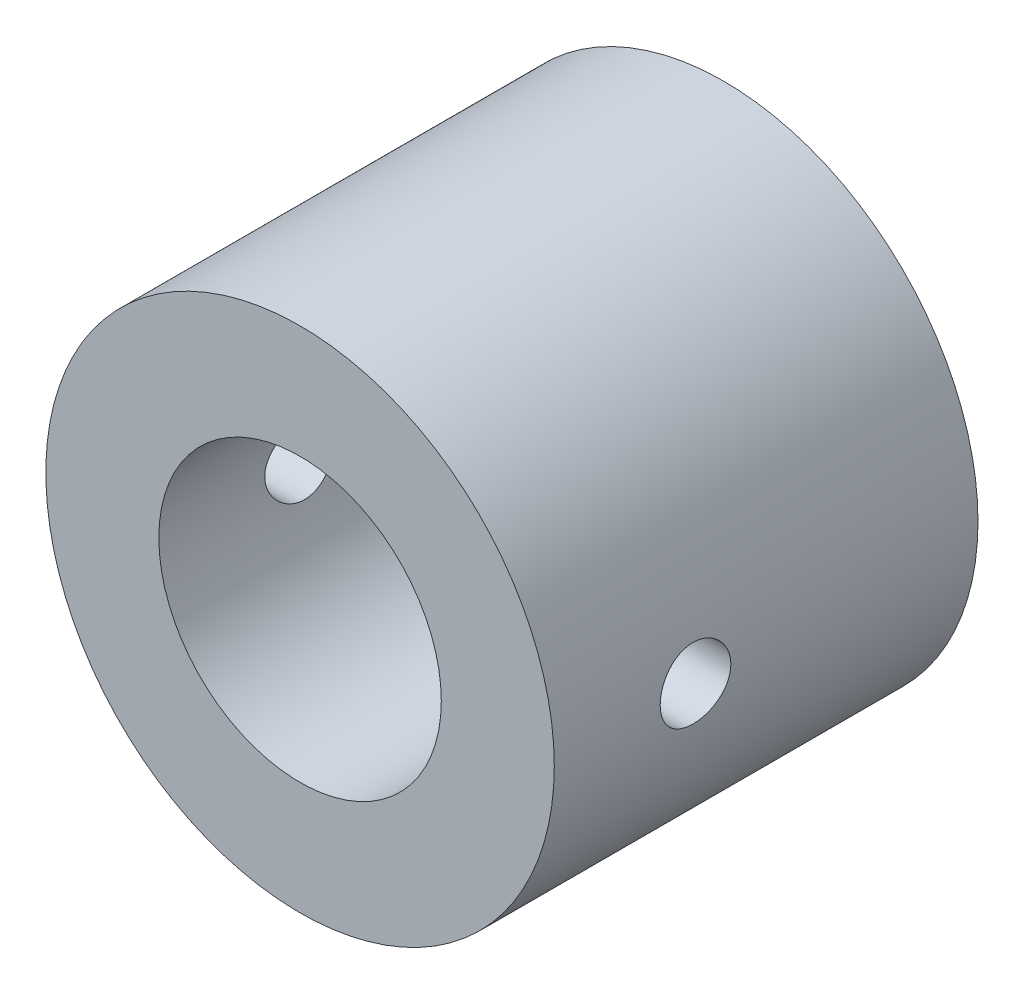
SolidWorks part; units mm, degrees
ref_plane "Plan de face" through (0, 0, 0) normal (0, 0, 1) x (1, 0, 0)
ref_plane "Plan de dessus" through (0, 0, 0) normal (0, 1, 0) x (1, 0, 0)
ref_plane "Plan de droite" through (0, 0, 0) normal (1, 0, 0) x (0, 0, -1)
sketch "Esquisse1" plane through (0, 0, 0) normal (0, 0, 1) x (1, 0, 0)
  circle A0 centre (0, 0) radius 5
  circle A1 centre (0, 0) radius 9
  dimension "D1" = 18
  dimension "D2" = 10
extrude "Boss.-Extru.1" add sketch "Esquisse1" along normal blind 15
sketch "Esquisse2" plane through (0, 0, 0) normal (1, 0, 0) x (0, 0, -1)
  line L0 (0, 0) -> (-15, 0) construction
  line L1 (-15, 9) -> (-15, -9) construction
  line L2 (-7.5, 8.0881) -> (-7.5, -7.4925) construction
ref_plane "Plan1" through (9, 0, 0) normal (1, 0, 0) x (0, 0, -1)
ref_plane "Plan2" through (-9, 0, 0) normal (1, 0, 0) x (0, 0, -1)
hole_wizard "Trou taraudé M31" positions "Esquisse5" profile "Esquisse6" tap size "M3" standard "DIN"
sketch "Esquisse5" plane through (9, 0, 0) normal (1, 0, 0) x (0, 0, -1)
  point P0 (-10, 0)
  point P5 (0, 0)
  dimension "D1" = 5
sketch "Esquisse6" plane through (9, 0, 10) normal (0, 1, 0) x (0, 0, -1)
  line L0 (0, 0) -> (0, 9.2511)
  line L1 (0, 9.2511) -> (1.25, 8.5)
  line L2 (1.25, 8.5) -> (1.25, 0)
  line L5 (1.25, 0) -> (0, 0)
  line L10 (0, 9.2511) -> (-1.25, 8.5) construction
  line L11 (0, -6.35) -> (0, 107.95) construction
  dimension "Diamètre du trou pour taraudage" = 2.5
  dimension "Profondeur du trou pour taraudage" = 8.5
  dimension "Angle de pointe" = 118
cosmetic thread "Filetage de perçage3" parameters "D1"=5.1588, "D2"=3
hole_wizard "Trou taraudé M32" positions "Esquisse7" profile "Esquisse8" tap size "M3" standard "DIN"
sketch "Esquisse7" plane through (-9, 0, 0) normal (1, 0, 0) x (0, 0, -1)
  point P0 (-10, 0)
  point P4 (0, 0)
  dimension "D1" = 5
sketch "Esquisse8" plane through (-9, 0, 10) normal (0, 1, 0) x (0, 0, 1)
  line L0 (0, 0) -> (0, 9.2511)
  line L1 (0, 9.2511) -> (1.25, 8.5)
  line L2 (1.25, 8.5) -> (1.25, 0)
  line L5 (1.25, 0) -> (0, 0)
  line L10 (0, 9.2511) -> (-1.25, 8.5) construction
  line L11 (0, -6.35) -> (0, 107.95) construction
  dimension "Diamètre du trou pour taraudage" = 2.5
  dimension "Profondeur du trou pour taraudage" = 8.5
  dimension "Angle de pointe" = 118
cosmetic thread "Filetage de perçage4" parameters "D1"=5.1588, "D2"=3
sketch "Esquisse9" plane through (0, 0, 0) normal (0, 0, -1) x (-1, 0, 0)
  circle A0 centre (0, 0) radius 8.1
  dimension "D1" = 16.2
extrude "Enlèv. mat.-Extru.1" cut sketch "Esquisse9" against normal blind 1
